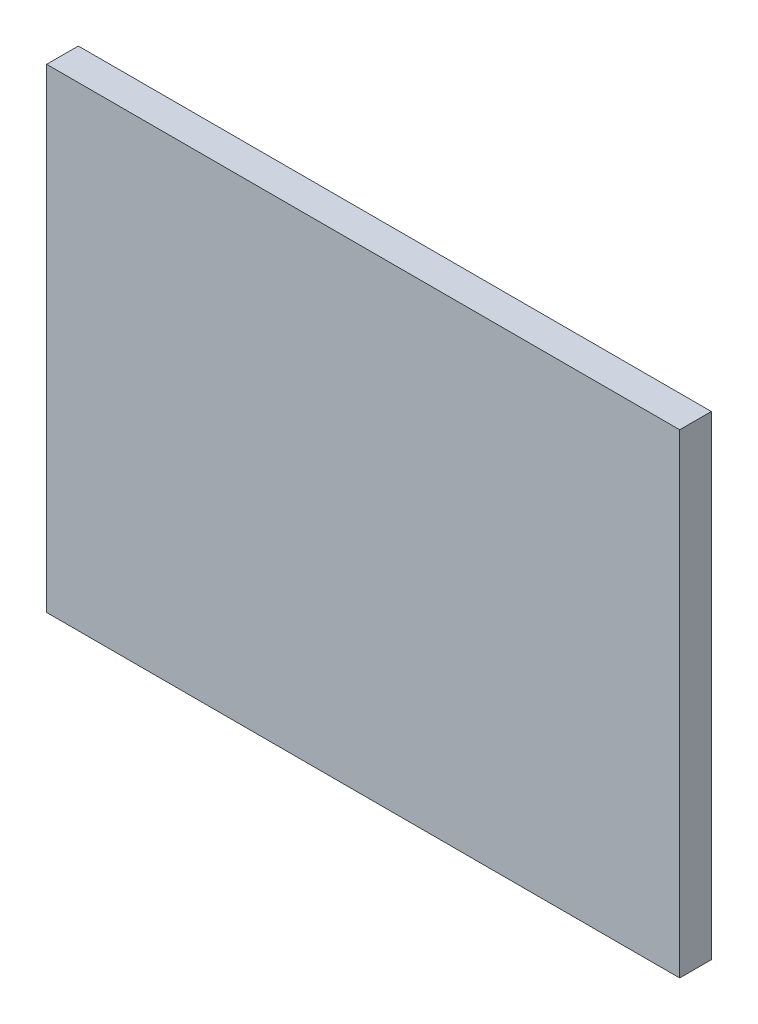
SolidWorks part; units mm, degrees
ref_plane "Front Plane" through (0, 0, 0) normal (0, 0, 1) x (1, 0, 0)
ref_plane "Top Plane" through (0, 0, 0) normal (0, 1, 0) x (1, 0, 0)
ref_plane "Right Plane" through (0, 0, 0) normal (1, 0, 0) x (0, 0, -1)
sketch "Sketch1" plane through (0, 0, 0) normal (0, 0, 1) x (1, 0, 0)
  line L1 (-10, -7.5) -> (10, -7.5)
  line L2 (-10, -7.5) -> (-10, 7.5)
  line L3 (-10, 7.5) -> (10, 7.5)
  line L4 (10, -7.5) -> (10, 7.5)
  line L5 (-10, -7.5) -> (10, 7.5) construction
  line L6 (-10, 7.5) -> (10, -7.5) construction
  point P0 (0, 0)
  dimension "D1" = 20
  dimension "D2" = 15
extrude "Boss-Extrude1" add sketch "Sketch1" along normal blind 1
